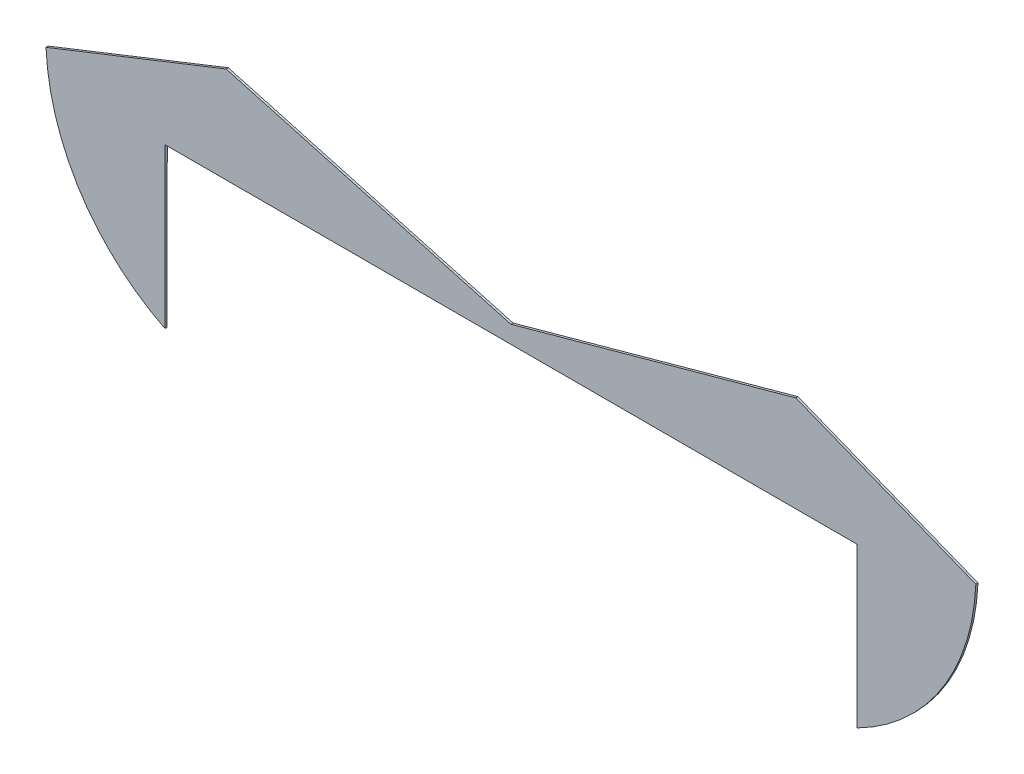
SolidWorks part; units mm, degrees
ref_plane "Alzado" through (0, 0, 0) normal (0, 0, 1) x (1, 0, 0)
ref_plane "Planta" through (0, 0, 0) normal (0, 1, 0) x (1, 0, 0)
ref_plane "Vista lateral" through (0, 0, 0) normal (1, 0, 0) x (0, 0, -1)
sketch "Model" plane through (0, 0, 0) normal (0, 0, 1) x (1, 0, 0)
  line L0 (18.5494, 16.9292) -> (35.0494, 16.9292)
  line L1 (18.5466, 9.5629) -> (18.5494, 16.9292)
  line L2 (50.5494, 16.9292) -> (50.5494, 9.5644)
  line L3 (35.0494, 16.9292) -> (50.5494, 16.9292)
  line L4 (56.0546, 18.078) -> (47.7251, 21.3754)
  line L5 (47.7251, 21.3754) -> (34.5491, 17.7362)
  line L6 (13.0401, 18.0772) -> (21.3734, 21.3758)
  line L7 (21.3734, 21.3758) -> (34.5491, 17.7362)
  arc A0 (14.4942, 13.2776) -> (18.5466, 9.5629) centre (22.9791, 18.4662) ccw
  arc A1 (50.5494, 9.5644) -> (54.6136, 13.3184) centre (46.0544, 18.5078) ccw
  arc A2 (54.6136, 13.3184) -> (56.0546, 18.078) centre (46.0544, 18.5078) ccw
  arc A3 (13.0401, 18.0772) -> (14.4942, 13.2776) centre (23.1397, 18.5169) ccw
extrude "Saliente-Extruir1" add sketch "Model" along normal blind 0.1
